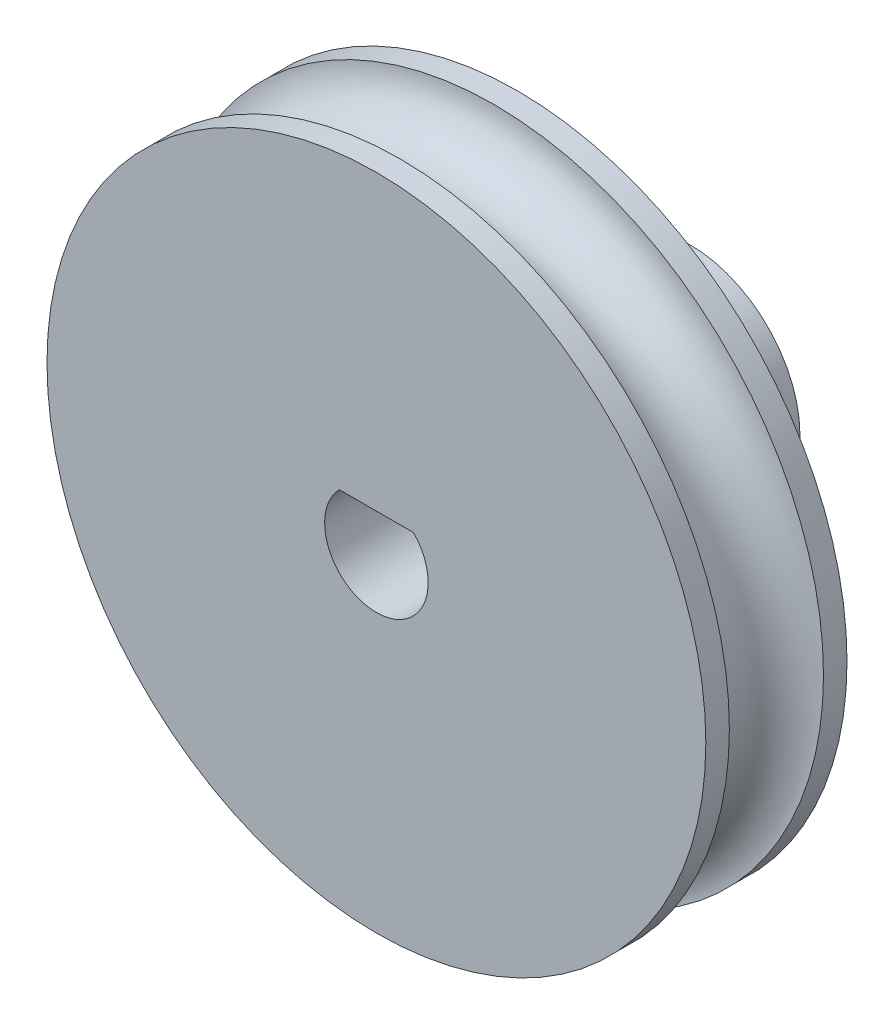
SolidWorks part; units mm, degrees
material "ABS"
ref_plane "Alzado" through (0, 0, 0) normal (0, 0, 1) x (1, 0, 0)
ref_plane "Planta" through (0, 0, 0) normal (0, 1, 0) x (1, 0, 0)
ref_plane "Vista lateral" through (0, 0, 0) normal (1, 0, 0) x (0, 0, -1)
sketch "Croquis1" plane through (0, 0, 0) normal (1, 0, 0) x (0, 0, -1)
  line L0 (0, 0) -> (50000, 0) construction
  line L1 (0, 0) -> (0, 10.5)
  line L2 (0, 10.5) -> (0.75, 10.5)
  line L3 (3.75, 10.5) -> (4.5, 10.5)
  line L4 (4.5, 10.5) -> (4.5, 3.5)
  line L5 (4.5, 3.5) -> (10, 3.5)
  line L6 (10, 3.5) -> (10, 0)
  line L7 (0, 0) -> (10, 0)
  arc A0 (0.75, 10.5) -> (3.75, 10.5) centre (2.25, 10.5) ccw
  dimension "D1" = 1.5
  dimension "D3" = 21
  dimension "D2" = 0.75
  dimension "D4" = 7
  dimension "D5" = 10
revolve "Revolución1" add sketch "Croquis1" angle 360 about L0
sketch "Croquis2" plane through (0, 0, -10) normal (0, 0, -1) x (-1, 0, 0)
  line L0 (-1.1619, 1.1) -> (1.1619, 1.1)
  arc A0 (-1.1619, 1.1) -> (1.1619, 1.1) centre (0, 0) ccw
  dimension "D1" = 3.2
  dimension "D2" = 1.1
extrude "Cortar-Extruir1" cut sketch "Croquis2" against normal through all
sketch "Croquis3" plane through (0, 0, -10) normal (0, 0, -1) x (-1, 0, 0)
  line L0 (-1.1832, 1.15) -> (1.1832, 1.15)
  line L1 (1.1619, 1.1) -> (-1.1619, 1.1) construction
  arc A0 (-1.1832, 1.15) -> (1.1832, 1.15) centre (0, 0) ccw
  arc A1 (-1.1619, 1.1) -> (1.1619, 1.1) centre (0, 0) ccw construction
  dimension "D1" = 0.05
  dimension "D2" = 0.05
extrude "Cortar-Extruir2" cut sketch "Croquis3" against normal up to surface (10 mm away) up to face at (0, -0.25, 0)
